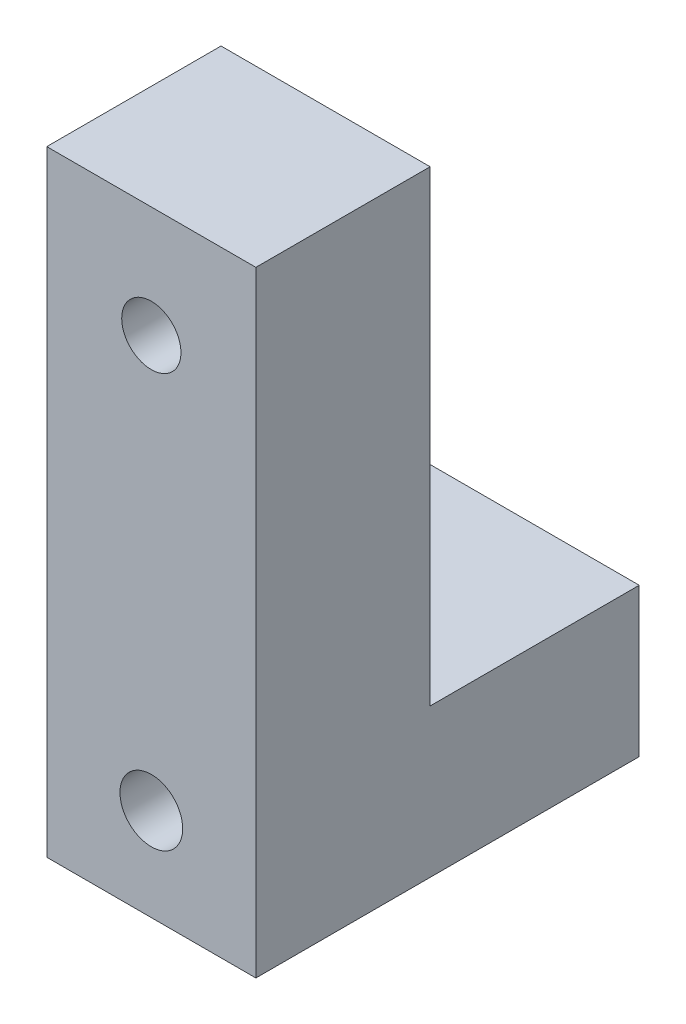
SolidWorks part; units mm, degrees
ref_plane "前视基准面" through (0, 0, 0) normal (0, 0, 1) x (1, 0, 0)
ref_plane "上视基准面" through (0, 0, 0) normal (0, 1, 0) x (1, 0, 0)
ref_plane "右视基准面" through (0, 0, 0) normal (1, 0, 0) x (0, 0, -1)
other "Configuration Table"
sketch "草图1" plane through (0, 0, 0) normal (1, 0, 0) x (0, 0, -1)
  line L6 (-18.5, 8) -> (-18.5, -13.3)
  line L7 (-73.5, 75) -> (-73.5, 8)
  line L8 (-48.5, 8) -> (-18.5, 8)
  line L13 (-73.5, 8) -> (-73.5, -13.3)
  line L15 (-48.5, 75) -> (-48.5, 8)
  line L17 (-48.5, 75) -> (-73.5, 75)
  line L20 (-18.5, -13.3) -> (-73.5, -13.3)
extrude "凸台-拉伸1" add sketch "草图1" along normal blind 30
sketch "草图2" plane through (0, 0, 18.5) normal (0, 0, -1) x (-1, 0, 0)
  circle A1 centre (-15, 0) radius 2.65
extrude "切除-拉伸1" cut sketch "草图2" against normal through all
ref_plane "基准面1" through (0, 0, 32.5) normal (0, 0, -1) x (-1, 0, 0)
sketch "草图4" plane through (0, 0, 32.5) normal (0, 0, -1) x (-1, 0, 0)
  circle A1 centre (-15, 0) radius 4.5
extrude "切除-拉伸3" cut sketch "草图4" against normal through all
sketch "草图5" plane through (0, 0, 48.5) normal (0, 0, -1) x (-1, 0, 0)
  circle A1 centre (-15, 59.0382) radius 4.25
extrude "切除-拉伸4" cut sketch "草图5" against normal through all
sketch "草图6" plane through (0, 0, 48.5) normal (0, 0, -1) x (-1, 0, 0)
  circle A2 centre (-15, 59.0382) radius 7
extrude "切除-拉伸5" cut sketch "草图6" against normal blind 8
